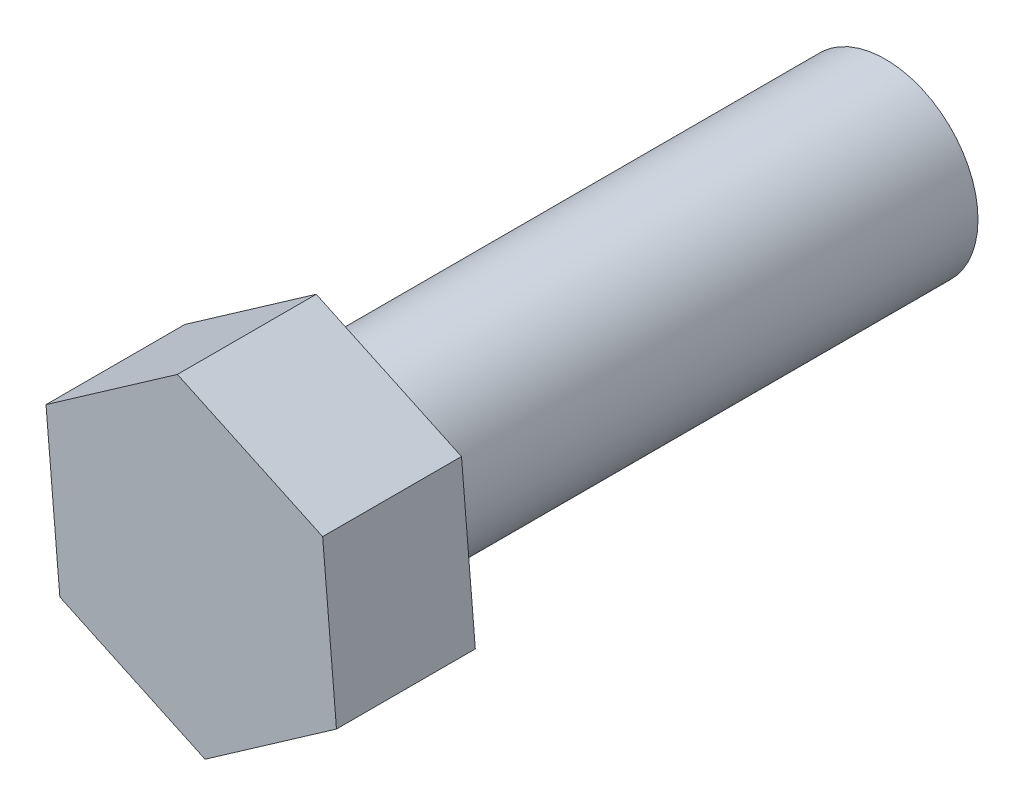
SolidWorks part; units mm, degrees
ref_plane "前视基准面" through (0, 0, 0) normal (0, 0, 1) x (1, 0, 0)
ref_plane "上视基准面" through (0, 0, 0) normal (0, 1, 0) x (1, 0, 0)
ref_plane "右视基准面" through (0, 0, 0) normal (1, 0, 0) x (0, 0, -1)
sketch "草图1" plane through (0, 0, 0) normal (0, 0, 1) x (1, 0, 0)
  line L1 (0.2992, -3.4512) -> (3.1384, -1.4665)
  line L2 (3.1384, -1.4665) -> (2.8392, 1.9847)
  line L3 (2.8392, 1.9847) -> (-0.2992, 3.4512)
  line L4 (-0.2992, 3.4512) -> (-3.1384, 1.4665)
  line L5 (-3.1384, 1.4665) -> (-2.8392, -1.9847)
  line L6 (-2.8392, -1.9847) -> (0.2992, -3.4512)
  circle A0 centre (0, 0) radius 3 construction
  dimension "D2" = 6
extrude "凸台-拉伸1" add sketch "草图1" along normal blind 3
sketch "草图2" plane through (0, 0, 0) normal (0, 0, -1) x (-1, 0, 0)
  circle A0 centre (0, 0) radius 2
  dimension "D1" = 4
extrude "凸台-拉伸2" add sketch "草图2" along normal blind 12
